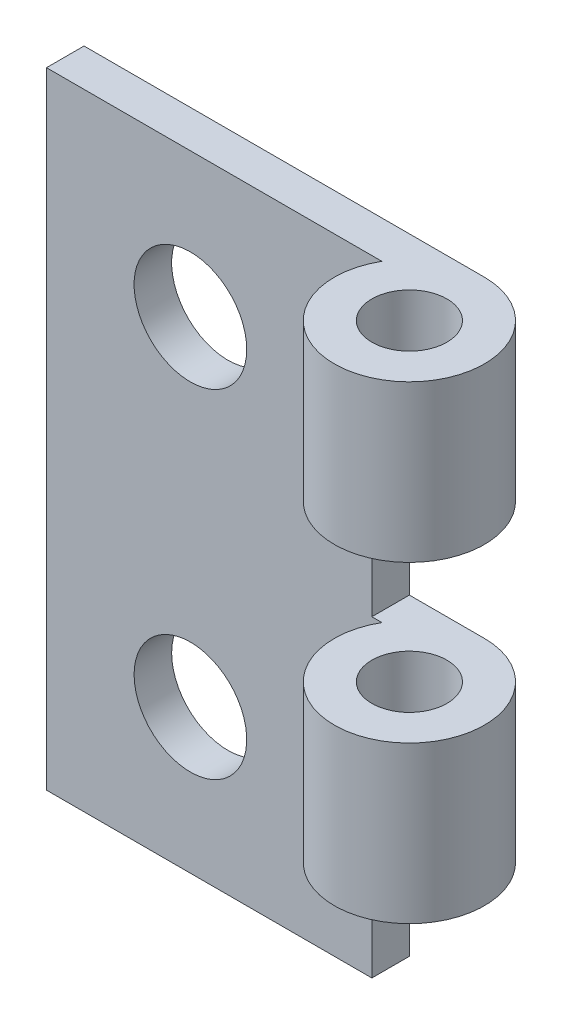
SolidWorks part; units mm, degrees
ref_plane "前视基准面" through (0, 0, 0) normal (0, 0, 1) x (1, 0, 0)
ref_plane "上视基准面" through (0, 0, 0) normal (0, 1, 0) x (1, 0, 0)
ref_plane "右视基准面" through (0, 0, 0) normal (1, 0, 0) x (0, 0, -1)
sketch "草图1" plane through (0, 0, 0) normal (0, 0, 1) x (1, 0, 0)
  line L0 (-6.5, 0) -> (6.5, 0) construction
  line L1 (6.5, -12.5) -> (-6.5, -12.5)
  line L2 (6.5, -12.5) -> (6.5, 12.5)
  line L3 (6.5, 12.5) -> (-6.5, 12.5)
  line L4 (-6.5, -12.5) -> (-6.5, 12.5)
  line L5 (6.5, -12.5) -> (-6.5, 12.5) construction
  line L6 (6.5, 12.5) -> (-6.5, -12.5) construction
  circle A0 centre (-0.75, 6.75) radius 2.25
  circle A1 centre (-0.75, -6.75) radius 2.25
  point P0 (0, 0)
  dimension "D3" = 5.75
  dimension "D5" = 4.5
  dimension "D1" = 25
  dimension "D2" = 13
  dimension "D4" = 5.75
extrude "凸台-拉伸1" add sketch "草图1" along normal blind 1.5
sketch "草图2" plane through (0, -12.5, 0) normal (0, -1, 0) x (1, 0, 0)
  line L0 (-6.5, 0) -> (6.5, 0) construction
  line L1 (6.5, 1.5) -> (6.5, 0) construction
  circle A0 centre (9.5, 3) radius 3
  circle A1 centre (9.5, 3) radius 1.5
extrude "凸台-拉伸2" add sketch "草图2" against normal blind 25 separate body
sketch "草图3" plane through (0, 0, 0) normal (0, 0, -1) x (-1, 0, 0)
  line L0 (-6.5, 12.5) -> (-9.5, 12.5)
  line L1 (-6.5, 12.5) -> (-12.5, 12.5) construction
  line L2 (-9.5, 12.5) -> (-9.5, -12.5)
  line L3 (-12.5, -12.5) -> (-6.5, -12.5) construction
  line L4 (-9.5, -12.5) -> (-6.5, -12.5)
  line L5 (-6.5, -12.5) -> (-6.5, 12.5)
extrude "凸台-拉伸3" add sketch "草图3" against normal blind 1.5
sketch "草图4" plane through (0, 0, 0) normal (0, 0, -1) x (-1, 0, 0)
  line L0 (-12.5, 0) -> (6.5, 0) construction
  line L1 (-12.5, 12.5) -> (-12.5, -12.5) construction
  line L2 (6.5, 12.5) -> (6.5, -12.5) construction
  line L3 (-12.5, -6.25) -> (6.5, -6.25) construction
  line L4 (6.5, -12.5) -> (-9.5, -12.5) construction
  line L5 (-12.5, -6.25) -> (-6.5, -6.25)
  line L6 (-6.5, -6.25) -> (-6.5, -12.5)
  line L7 (-6.5, -12.5) -> (-12.5, -12.5)
  line L8 (-12.5, -12.5) -> (-12.5, -6.25)
  line L9 (-12.5, 0) -> (-12.5, 6.25)
  line L10 (-12.5, 6.25) -> (-6.5, 6.25)
  line L11 (-6.5, 6.25) -> (-6.5, 0)
  line L12 (-6.5, 0) -> (-12.5, 0)
  dimension "D1" = 6.25
  dimension "D2" = 6
  dimension "D3" = 6.25
  dimension "D4" = 6
extrude "切除-拉伸1" cut sketch "草图4" against normal through all
sketch "草图6" plane through (0, 0, 0) normal (0, 0, -1) x (-1, 0, 0)
  line L0 (0.75, -6.75) -> (0.75, 6.75) construction
